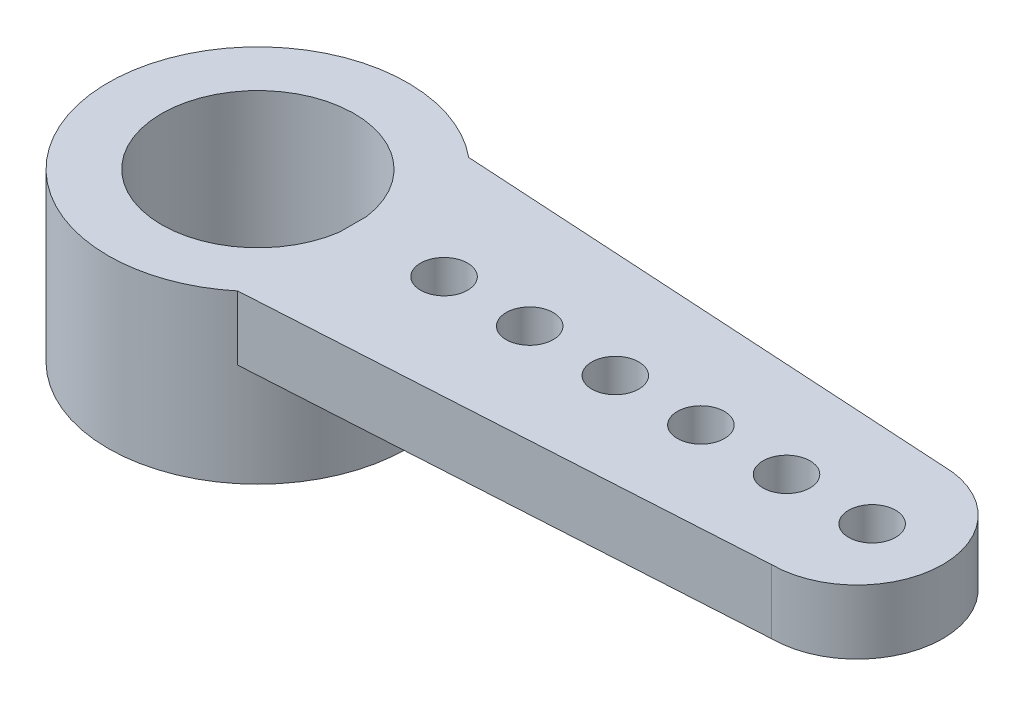
SolidWorks part; units mm, degrees
ref_plane "Front Plane" through (0, 0, 0) normal (0, 0, 1) x (1, 0, 0)
ref_plane "Top Plane" through (0, 0, 0) normal (0, 1, 0) x (1, 0, 0)
ref_plane "Right Plane" through (0, 0, 0) normal (1, 0, 0) x (0, 0, -1)
sketch "Sketch1" plane through (0, 0, 0) normal (0, 1, 0) x (1, 0, 0)
  circle A0 centre (0, 0) radius 3.5
  circle A1 centre (0, 0) radius 2.25
  dimension "D1" = 7
  dimension "D2" = 4.5
extrude "Boss-Extrude1" add sketch "Sketch1" against normal blind 3.9
sketch "Sketch2" plane through (0, 0, 0) normal (0, 1, 0) x (1, 0, 0)
  line L0 (-3.5, 0) -> (16, 0) construction
  line L1 (14, 2) -> (2.2271, 2.7)
  line L2 (2.2271, 2.7) -> (2.2271, -2.7)
  line L3 (2.2271, -2.7) -> (14, -2)
  line L4 (0, 2.25) -> (0, -2.25) construction
  circle A0 centre (0, 0) radius 3.5 construction
  circle A1 centre (14, 0) radius 2
  circle A2 centre (0, 0) radius 2.25 construction
  dimension "D1" = 4
  dimension "D2" = 5.4
  dimension "D3" = 19.5
extrude "Boss-Extrude2" add sketch "Sketch2" against normal blind 1.5 contours A1 L1 L2 L3 | A1
sketch "Sketch3" plane through (0, 0, 0) normal (0, 1, 0) x (1, 0, 0)
  line L0 (0, 0) -> (16, 0) construction
  arc A0 (14, -2) -> (14, 2) centre (14, 0) ccw construction
  circle A1 centre (14.35, 0) radius 0.55
  dimension "D1" = 1.1
  dimension "D2" = 1.65
extrude "Cut-Extrude1" cut sketch "Sketch3" against normal blind 1.5
pattern_linear "LPattern1" count 6 spacing 2 along (-1, 0, 0) of "Cut-Extrude1"
